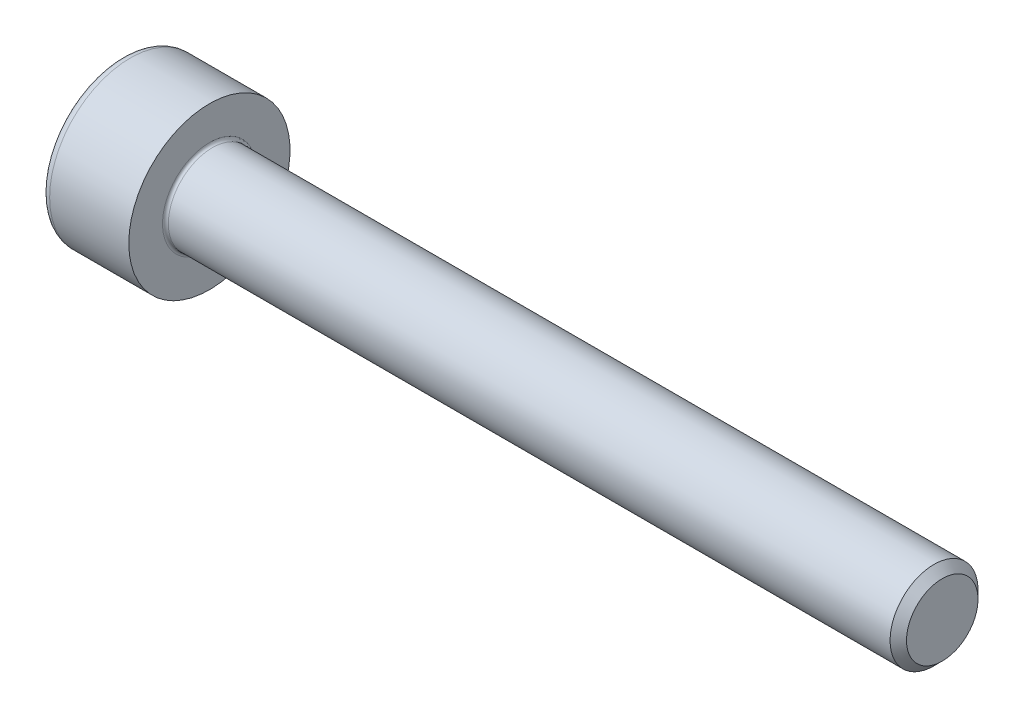
SolidWorks part; units mm, degrees
revolve "Base-Revolve" add sketch "BodySke"
sketch "BodySke" plane through (0, 0, 0) normal (0, 0, 1) x (1, 0, 0)
  line L0 (0, 0) -> (0, 2.75)
  line L1 (0, 2.75) -> (3, 2.75)
  line L2 (3, 2.75) -> (3, 1.5)
  line L3 (3, 1.5) -> (27.7195, 1.5)
  line L4 (28, 1.2195) -> (28, 0)
  line L5 (28, 0) -> (0, 0)
  line L6 (-31.75, 0) -> (127, 0) construction
  line L8 (28, 1.2195) -> (27.7195, 1.5)
  line L10 (28, -1.2195) -> (27.7195, -1.5) construction
  line L11 (3.5, 9.525) -> (3.5, 3.175) construction
  line L12 (23, 9.525) -> (23, 3.175) construction
  line L13 (-32, 9.525) -> (-32, 3.175) construction
  dimension "Head_ht" = 3
  dimension "Length" = 25
  dimension "Body_ch_ang" = 45
  dimension "Diameter" = 3
  dimension "Minor_dia" = 2.439
  dimension "Advance" = 0.5
  dimension "Thread_nom" = 5
  dimension "Thread_length" = 60
  dimension "Head_dia" = 5.5
cosmetic thread "ThreadCosmetic" [suppressed]
fillet "Fillet1" radius 0.1 1 edges at (3, 0, 1.5)
fillet "Fillet2" radius 0.3 1 edges at (0, 0, 2.75)
ref_plane "Plane1" through (0, 0, 0) normal (0, 0, 1) x (1, 0, 0)
ref_plane "Plane2" through (0, 0, 0) normal (0, 1, 0) x (1, 0, 0)
ref_plane "Plane3" through (0, 0, 0) normal (1, 0, 0) x (0, 0, -1)
other "Configuration Table"
sketch "Sketch2" plane through (0, 0, 0) normal (0, 0, 1) x (1, 0, 0)
  line L0 (0, 1.26) -> (1.3, 1.26)
  line L1 (1.3, 1.26) -> (2.0275, 0)
  line L2 (-31.75, 0) -> (127, 0) construction
  line L3 (2.0275, 0) -> (0, 0)
  line L4 (0, 0) -> (0, 1.26)
  line L6 (0, 0) -> (47.625, 0) construction
  dimension "D1" = 1.26
  dimension "D2" = 60
  dimension "Depth" = 1.3
revolve "Hex-PreBroach" cut sketch "Sketch2" angle 360 about L6
sketch "Sketch3" plane through (0, 0, 0) normal (-1, 0, 0) x (0, 0.5, 0.866)
  line L0 (0.7275, 1.26) -> (-0.7275, 1.26)
  line L1 (-0.7275, 1.26) -> (-1.4549, 0)
  line L2 (0.7275, 1.26) -> (1.4549, 0)
  line L3 (0.7275, -1.26) -> (1.4549, 0)
  line L4 (0.7275, -1.26) -> (-0.7275, -1.26)
  line L5 (-0.7275, -1.26) -> (-1.4549, 0)
  dimension "D1" = 1.26
  dimension "D2" = 1.26
  dimension "Hex_size" = 2.52
extrude "Hex" cut sketch "Sketch3" against normal blind 1.3
sketch "ThdSchSke" plane through (0, 0, 0) normal (0, 0, 1) x (1, 0, 0)
  line L0 (23, -1.2195) -> (22.8036, -1.5)
  line L1 (23, -1.2195) -> (23.1964, -1.5)
  line L2 (23.1964, -1.5) -> (23.1964, -1.875)
  line L3 (-3.175, 0) -> (5.1513, 0) construction
  line L4 (0, 2.45) -> (0, -2.45) construction
  line L5 (23.1964, -1.875) -> (22.8036, -1.875)
  line L6 (22.8036, -1.875) -> (22.8036, -1.5)
  dimension "Thread_minor" = 2.439
  dimension "Diameter" = 3
  dimension "Start" = 23
revolve "ThreadSchematic" [suppressed] cut sketch "ThdSchSke" angle 360 about L3
pattern_linear "ThdSchPat" [suppressed]
equation "\"D2@Sketch3\" = \"Hex_size@Sketch3\" / 2"
equation "\"D1@Sketch3\" = \"Hex_size@Sketch3\" / 2"
equation "\"D1@Sketch2\" = \"Hex_size@Sketch3\" / 2"
equation "\"Thread_minor@ThreadCosmetic\"  =  \"Minor_dia@BodySke\""
equation "\"Depth@Sketch2\" =  \"Key_eng@Hex\""
equation "\"Thread_length@ThreadCosmetic\" = ((sgn( (\"Length@BodySke\" - \"Advance@BodySke\" * 3.0) - \"Thread_nom@BodySke\" )-1)*( (\"Length@BodySke\" - \"Advance@BodySke\" * 3.0) - \"Thread_nom@BodySke\" ))/-2+ \"Thread_nom@BodySke\""
equation "\"Thread_minor@ThdSchSke\" = \"Minor_dia@BodySke\""
equation "\"Diameter@ThdSchSke\" = \"Diameter@BodySke\""
equation "\"Overcut@ThdSchSke\" = \"Diameter@BodySke\" * 1.25"
equation "\"Start@ThdSchSke\" = \"Head_ht@BodySke\" + \"Length@BodySke\" - \"Thread_length@ThreadCosmetic\"  '---Non-countersunk---"
equation "\"Num_threads@ThdSchPat\" = int( \"Thread_length@ThreadCosmetic\" / \"Advance@BodySke\" + 0.999 )  + 1"
equation "\"Advance@ThdSchPat\" = \"Thread_length@ThreadCosmetic\" /  (\"Num_threads@ThdSchPat\" - 1) 'relax it"
equation "\"Num_threads@ThdSchPat\" = \"Num_threads@ThdSchPat\" - sgn( \"Num_threads@ThdSchPat\" - 1) '---chamfered tips only---"
